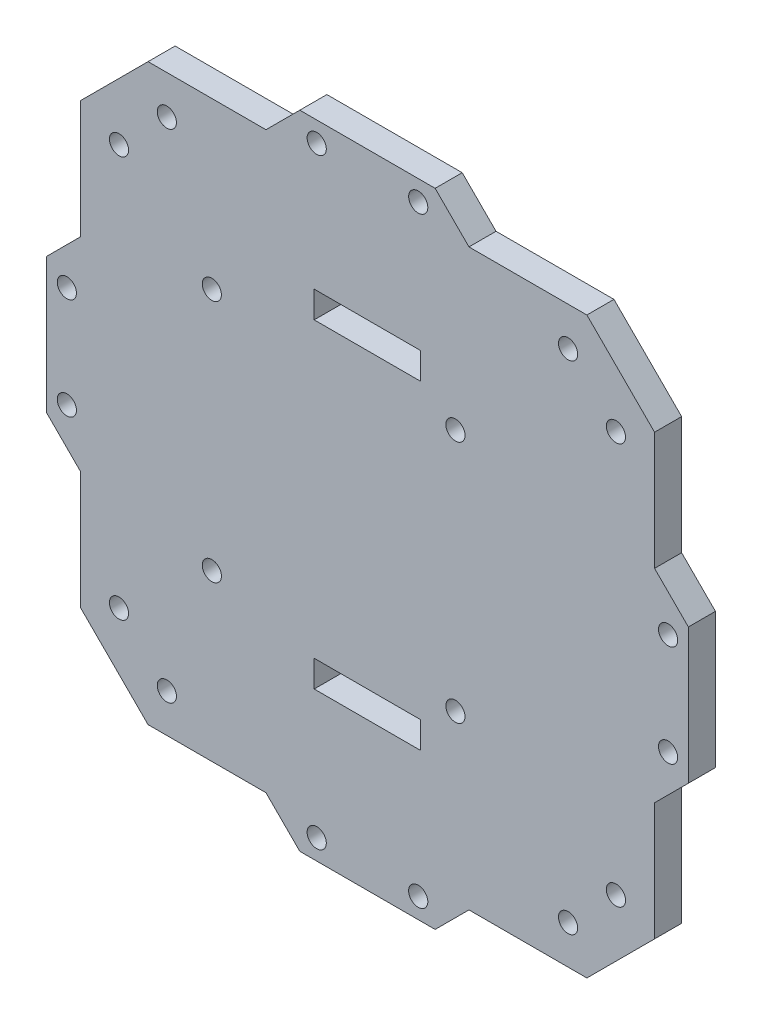
SolidWorks part; units mm, degrees
material "PETG CF"
ref_plane "Front Plane" through (0, 0, 0) normal (1, 0, 0) x (0, 1, 0)
ref_plane "Top Plane" through (0, 0, 0) normal (0, 0, 1) x (0, 1, 0)
ref_plane "Right Plane" through (0, 0, 0) normal (0, 1, 0) x (-1, 0, 0)
sketch "Sketch1" plane through (0, 0, 0) normal (0, 0, 1) x (0, 1, 0)
  line L5 (-41.1815, 53.8815) -> (-19.05, 53.8815)
  line L8 (53.8815, -53.8815) -> (19.05, -53.8815) construction
  line L17 (53.8815, -53.8815) -> (53.8815, -19.05) construction
  line L18 (53.8815, 53.8815) -> (19.05, 53.8815) construction
  line L19 (-53.8815, -53.8815) -> (-53.8815, -19.05) construction
  line L26 (-53.8815, 53.8815) -> (53.8815, -53.8815) construction
  line L27 (53.8815, 53.8815) -> (-53.8815, -53.8815) construction
  line L28 (41.1815, 53.8815) -> (53.8815, 41.1815)
  line L29 (53.8815, 41.1815) -> (53.8815, 19.05)
  line L30 (53.8815, -41.1815) -> (41.1815, -53.8815)
  line L31 (41.1815, -53.8815) -> (19.05, -53.8815)
  line L32 (-41.1815, -53.8815) -> (-53.8815, -41.1815)
  line L33 (-53.8815, -41.1815) -> (-53.8815, -19.05)
  line L34 (-53.8815, 41.1815) -> (-41.1815, 53.8815)
  line L35 (-46.6335, -37.6533) -> (-37.6533, -46.6335) construction
  line L40 (-27.5, -10) -> (27.5, -10) construction
  line L42 (0, 63.811) -> (0, -81.2604) construction
  line L43 (-47.3805, 0) -> (65.1963, 0) construction
  line L50 (-22.86, 29.21) -> (22.86, 29.21) construction
  line L51 (-22.86, 29.21) -> (-22.86, -16.51) construction
  line L52 (-22.86, -16.51) -> (22.86, -16.51) construction
  line L53 (22.86, 29.21) -> (22.86, -16.51) construction
  line L54 (-22.86, 29.21) -> (22.86, -16.51) construction
  line L55 (-22.86, -16.51) -> (22.86, 29.21) construction
  line L59 (-19.05, -53.8815) -> (-12.7, -60.2315)
  line L60 (-12.7, -60.2315) -> (12.7, -60.2315)
  line L61 (-32.5, 10) -> (-27.5, 10)
  line L62 (-32.5, 10) -> (-32.5, -10)
  line L63 (-32.5, -10) -> (-27.5, -10)
  line L64 (-27.5, 10) -> (-27.5, -10)
  line L65 (27.5, 10) -> (32.5, 10)
  line L66 (27.5, 10) -> (27.5, -10)
  line L67 (27.5, -10) -> (32.5, -10)
  line L68 (32.5, 10) -> (32.5, -10)
  line L69 (12.7, -60.2315) -> (19.05, -53.8815)
  line L78 (-19.05, -53.8815) -> (-53.8815, -53.8815) construction
  line L79 (-19.05, -53.8815) -> (-41.1815, -53.8815)
  line L80 (-9.525, -56.4215) -> (9.525, -56.4215) construction
  line L81 (-60.2315, -12.7) -> (-53.8815, -19.05)
  line L82 (-60.2315, 12.7) -> (-60.2315, -12.7)
  line L83 (-53.8815, 19.05) -> (-60.2315, 12.7)
  line L84 (-12.7, 60.2315) -> (-19.05, 53.8815)
  line L85 (12.7, 60.2315) -> (-12.7, 60.2315)
  line L86 (19.05, 53.8815) -> (12.7, 60.2315)
  line L87 (60.2315, 12.7) -> (53.8815, 19.05)
  line L88 (60.2315, -12.7) -> (60.2315, 12.7)
  line L89 (53.8815, -19.05) -> (60.2315, -12.7)
  line L90 (-53.8815, 19.05) -> (-53.8815, 41.1815)
  line L91 (-53.8815, 19.05) -> (-53.8815, 53.8815) construction
  line L92 (19.05, 53.8815) -> (41.1815, 53.8815)
  line L93 (-19.05, 53.8815) -> (-53.8815, 53.8815) construction
  line L94 (53.8815, 19.05) -> (53.8815, 53.8815) construction
  line L95 (53.8815, -19.05) -> (53.8815, -41.1815)
  circle A0 centre (-46.6335, -37.6533) radius 1.8
  circle A1 centre (-37.6533, -46.6335) radius 1.8
  circle A6 centre (46.6335, -37.6533) radius 1.8
  circle A7 centre (37.6533, -46.6335) radius 1.8
  circle A8 centre (-46.6335, 37.6533) radius 1.8
  circle A9 centre (-37.6533, 46.6335) radius 1.8
  circle A10 centre (37.6533, 46.6335) radius 1.8
  circle A11 centre (46.6335, 37.6533) radius 1.8
  circle A16 centre (-22.86, -16.51) radius 1.8
  circle A17 centre (22.86, -16.51) radius 1.8
  circle A18 centre (22.86, 29.21) radius 1.8
  circle A19 centre (-22.86, 29.21) radius 1.8
  circle A20 centre (9.525, -56.4215) radius 1.8
  circle A21 centre (-9.525, -56.4215) radius 1.8
  circle A22 centre (-56.4215, -9.525) radius 1.8
  circle A23 centre (-56.4215, 9.525) radius 1.8
  circle A24 centre (-9.525, 56.4215) radius 1.8
  circle A25 centre (9.525, 56.4215) radius 1.8
  circle A26 centre (56.4215, 9.525) radius 1.8
  circle A27 centre (56.4215, -9.525) radius 1.8
  point P0 (0, 0)
  point P5 (0, 0)
  point P8 (0, 0)
  point P20 (0, 6.35)
  point P40 (-42.1434, -42.1434)
  point P47 (0, -42)
  point P63 (-30, -10)
  point P64 (-27.5, 0)
  point P65 (0, -10)
  point P67 (0, -60.2315)
  point P70 (0, -56.4215)
  point P95 (0, 0)
  dimension "D4" = 3.6
  dimension "D13" = 3.6
  dimension "D20" = 3.6
  dimension "D1" = 152.4
  dimension "D5" = 12.7
  dimension "D6" = 12.7
  dimension "D8" = 45
  dimension "D9" = 45.72
  dimension "D10" = 45.72
  dimension "D11" = 7.62
  dimension "D3" = 6.35
  dimension "D15" = 42
  dimension "D16" = 5
  dimension "D17" = 20
  dimension "D18" = 65
  dimension "D7" = 38.1
  dimension "D12" = 6.35
  dimension "D14" = 6.35
  dimension "D19" = 6.35
  dimension "D21" = 3.81
  dimension "D22" = 19.05
  dimension "D24" = 107.7631
  dimension "D23" = 4
extrude "Boss-Extrude1" add sketch "Sketch1" along normal blind 5.08
equation "\"Width\"= sqr ( ( \"Diagonal\" ^ 2 ) / 2 )"
equation "\"depth\"= 0.2in"
equation "\"D1@Boss-Extrude1\"=\"depth\""
equation "\"Aluminum Standoff Radius\"= 3mm'Radius of the standoffs for the wings (M5 screws)"
equation "\"Corner Spacing\"= 25in"
equation "\"Diagonal\"= 6in'Diagonal measurements of the standoff"
equation "\"D1@Sketch1\"=\"Diagonal\""
equation "\"D4@Sketch1\" = \"Aluminum Standoff Radius\" + \"Tolerance\""
equation "\"Wing Standoff Spacing\"= 0.5in"
equation "\"D6@Sketch1\"=\"Wing Standoff Spacing\""
equation "\"Standoff Hole Offset\"= .4in"
equation "\"Tolerance\"= 0.6mm"
equation "\"Nylon Standoff Radius\"= 3mm"
equation "\"D13@Sketch1\" = \"Nylon Standoff Radius\" + \"Tolerance\""
equation "\"D20@Sketch1\"= \"Aluminum Standoff Radius\" + \"Tolerance\""
equation "\"D24@Sketch1\"=\"Width\""
equation "\"Le\"=6"
